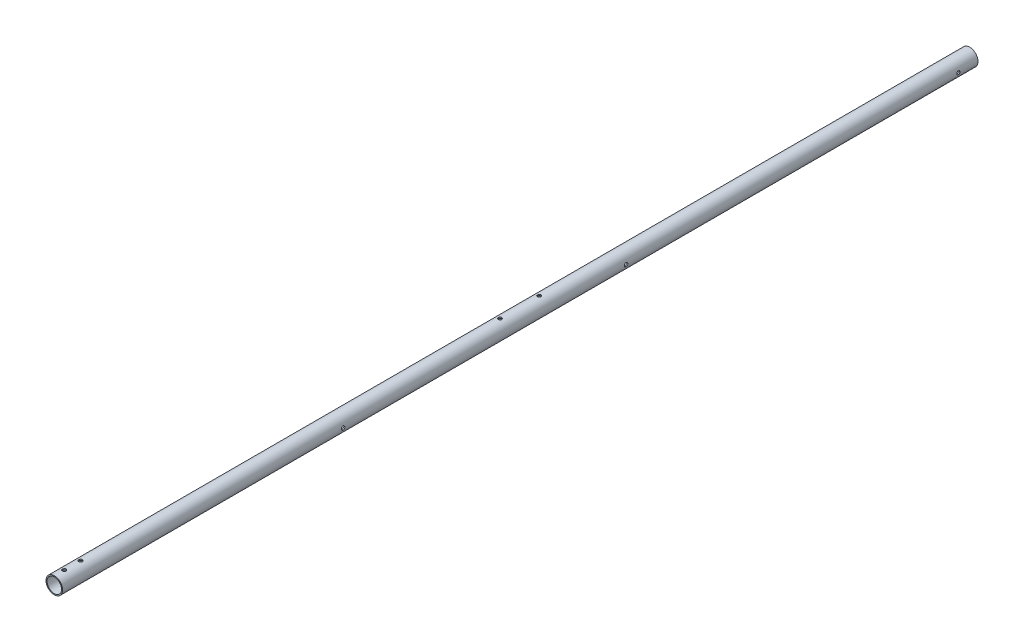
SolidWorks part; units mm, degrees
material "1060 Alloy"
ref_plane "Front Plane" through (0, 0, 0) normal (0, 0, 1) x (1, 0, 0)
ref_plane "Top Plane" through (0, 0, 0) normal (0, 1, 0) x (1, 0, 0)
ref_plane "Right Plane" through (0, 0, 0) normal (1, 0, 0) x (0, 0, -1)
sketch "Sketch2" plane through (0, 0, 0) normal (0, 0, 1) x (1, 0, 0)
  circle A0 centre (0, 0) radius 12.7
  circle A1 centre (0, 0) radius 11.1125
  dimension "D1" = 25.4
  dimension "D2" = 22.225
extrude "Boss-Extrude1" add sketch "Sketch2" along normal blind 1400
sketch "Sketch3" plane through (0, 0, 0) normal (0, 1, 0) x (1, 0, 0)
  line L0 (0, -1400) -> (0, -1392.75) construction
  line L1 (-12.7, -1400) -> (12.7, -1400) construction
  line L2 (0, -1392.75) -> (0, -1372.75) construction
  dimension "D1" = 7.25
  dimension "D2" = 20
hole_wizard "M5 Clearance Hole1" positions "Sketch4" profile "Sketch6" hole size "M5" standard "AS"
sketch "Sketch4" plane through (0, 0, 0) normal (0, 1, 0) x (1, 0, 0)
  line L0 (-12.7, -1400) -> (12.7, -1400) construction
  point P0 (0, -1385)
  point P6 (0, -1360)
  dimension "D1" = 25
  dimension "D2" = 15
sketch "Sketch6" plane through (0, 0, 1385) normal (1, 0, 0) x (0, 0, -1)
  line L0 (0, 0) -> (0, 12.7)
  line L1 (0, 12.7) -> (2.75, 12.7)
  line L2 (2.75, 12.7) -> (2.75, 0)
  line L5 (2.75, 0) -> (0, 0)
  line L11 (0, -6.35) -> (0, 107.95) construction
  dimension "Thru Hole Dia." = 5.5
  dimension "Thru Hole Depth" = 12.7
mirror "Mirror1" about plane through (0, 0, 0) normal (0, 1, 0) of "M5 Clearance Hole1"
sketch "Sketch7" plane through (0, 0, 0) normal (0, 1, 0) x (1, 0, 0)
  circle A0 centre (0, -658.4552) radius 2.65
  circle A1 centre (0, -718.4552) radius 2.65
  circle A2 centre (0, -718.4552) radius 2.65 construction
  point P0 (0, -658.4552)
  point P1 (0, -718.4552)
extrude "Cut-Extrude1" cut sketch "Sketch7" against normal through all both and the other way through all
sketch "Sketch8" plane through (0, 0, 0) normal (1, 0, 0) x (0, 0, -1)
  circle A0 centre (-30, 0) radius 2.5
  dimension "D1" = 5
  dimension "D2" = 30
extrude "Cut-Extrude2" cut sketch "Sketch8" against normal through all both and the other way through all
sketch "Sketch9" plane through (0, 0, 0) normal (1, 0, 0) x (0, 0, -1)
  circle A0 centre (-538.255, 0) radius 2.75
  circle A1 centre (-538.255, 0) radius 2.75 construction
  circle A2 centre (-970.9552, 0) radius 2.75
extrude "Cut-Extrude3" cut sketch "Sketch9" against normal through all both and the other way through all
equation "\"keelOutDiameter\"= 1in"
equation "\"keelInDiameter\"= \"keelOutDiameter\" - 0.125in"
equation "\"D1@Sketch2\"=\"keelOutDiameter\""
equation "\"D2@Sketch2\"=\"keelInDiameter\""
equation "\"frontBoltClearance\"= 7.25mm"
equation "\"D1@Sketch3\"=\"frontBoltClearance\""
equation "\"betweenBoltsDistance\"= 20mm"
equation "\"D2@Sketch3\"=\"betweenBoltsDistance\""
equation "\"wingLength\"= 1.4m"
equation "\"D1@Boss-Extrude1\"=\"wingLength\""
